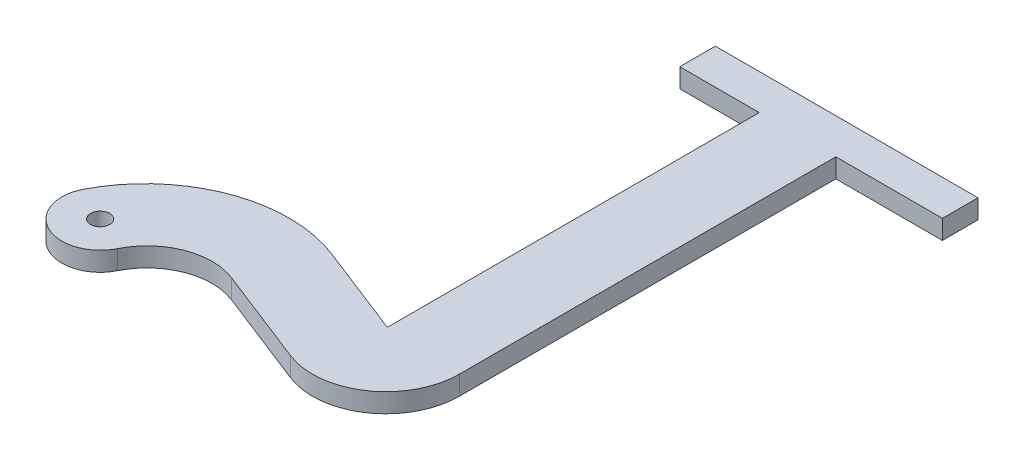
SolidWorks part; units mm, degrees
ref_plane "Plan de face" through (0, 0, 0) normal (0, 0, 1) x (1, 0, 0)
ref_plane "Plan de dessus" through (0, 0, 0) normal (0, 1, 0) x (1, 0, 0)
ref_plane "Plan de droite" through (0, 0, 0) normal (1, 0, 0) x (0, 0, -1)
sketch "Esquisse1" plane through (0, 0, 0) normal (0, 1, 0) x (1, 0, 0)
  line L0 (30.4165, 3.8757) -> (55.8233, -6.0594)
  line L1 (82, 11.8114) -> (82, 110.1231)
  line L2 (82, 110.1231) -> (109.8322, 110.1231)
  line L3 (62, 110.1231) -> (62, 13)
  line L4 (62, 13) -> (38.1731, 22.3173)
  line L5 (109.8322, 110.1231) -> (109.8322, 119.415)
  line L6 (109.8322, 119.415) -> (41.2524, 119.415)
  line L7 (41.2524, 119.415) -> (41.2524, 110.1231)
  line L8 (41.2524, 110.1231) -> (62, 110.1231)
  circle A0 centre (0, 0) radius 2.5
  arc A1 (8.9669, -4.4317) -> (-8.8821, 4.5994) centre (0, 0) cw
  arc A2 (8.9669, -4.4317) -> (30.4165, 3.8757) centre (24.2201, -11.9702) cw
  arc A3 (55.8233, -6.0594) -> (82, 11.8114) centre (62.8115, 11.8114) ccw
  arc A5 (38.1731, 22.3173) -> (-8.8821, 4.5994) centre (24.4876, -12.6803) ccw
  point P10 (0, 0)
  point P13 (59.8786, 108.6458)
  point P20 (60.676, 14.8492)
  point P21 (62.9886, 110.1231)
  point P22 (19.1536, 5.4576)
  point P23 (19.1033, 4.2565)
  point P24 (29.8004, 4.4172)
  point P25 (30.1836, 19.9613)
  point P26 (0, 0)
  point P27 (19.1033, 3.8757)
  point P29 (0, 0)
  point P30 (109.8322, 127.4015)
  point P31 (41.2524, 119.415)
  dimension "D1" = 5
  dimension "D3" = 13
  dimension "D5" = 20
  dimension "D2" = 10.0023
  dimension "D4" = 62
  dimension "D6" = 20
extrude "Boss.-Extru.1" add sketch "Esquisse1" along normal blind 5
